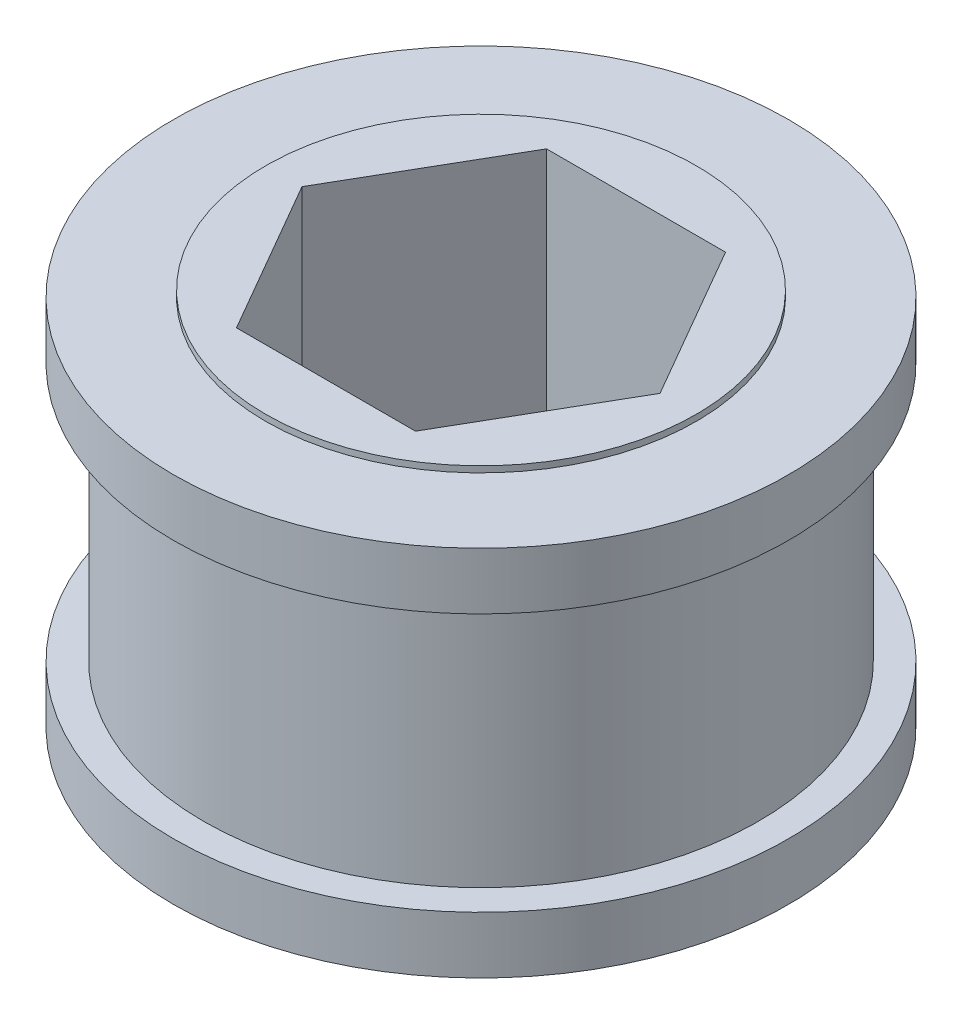
SolidWorks part; units mm, degrees
ref_plane "Front Plane" through (0, 0, 0) normal (0, 0, 1) x (1, 0, 0)
ref_plane "Top Plane" through (0, 0, 0) normal (0, 1, 0) x (1, 0, 0)
ref_plane "Right Plane" through (0, 0, 0) normal (1, 0, 0) x (0, 0, -1)
ref_axis "Axis1" through (0, 55, 0) along (0, -1, 0)
sketch "Sketch2" plane through (0, 0, 0) normal (1, 0, 0) x (0, 0, -1)
  line L0 (2.54, -3.2131) -> (8.89, -3.2131)
  line L1 (8.89, -3.2131) -> (8.89, -3.4671)
  line L2 (8.89, -3.4671) -> (12.7, -3.4671)
  line L3 (12.7, -3.4671) -> (12.7, -5.8166)
  line L5 (11.4554, -5.8166) -> (11.4554, -16.4846)
  line L7 (12.7, -16.4846) -> (12.7, -18.8341)
  line L8 (12.7, -18.8341) -> (8.89, -18.8341)
  line L9 (8.89, -18.8341) -> (8.89, -19.0881)
  line L10 (8.89, -19.0881) -> (2.54, -19.0881)
  line L11 (11.4554, -5.8166) -> (12.7, -5.8166)
  line L13 (2.54, -19.0881) -> (2.54, -3.2131)
  line L14 (0, 55) -> (0, -55) construction
  line L17 (11.4554, -16.4846) -> (12.7, -16.4846)
  dimension "D1" = 15.875
  dimension "D2" = 2.54
  dimension "D3" = 12.7
  dimension "D4" = 6.35
  dimension "D5" = 0.254
  dimension "D6" = 10.668
  dimension "D7" = 11.4554
revolve "Revolve1" add sketch "Sketch2" angle 360 about axis through (0, 55, 0) along (0, -1, 0)
sketch "Sketch3" plane through (0, -3.2131, 0) normal (0, 1, 0) x (1, 0, 0)
  line L1 (3.6955, 6.4008) -> (-3.6955, 6.4008)
  line L2 (-3.6955, 6.4008) -> (-7.391, 0)
  line L3 (-7.391, 0) -> (-3.6955, -6.4008)
  line L4 (-3.6955, -6.4008) -> (3.6955, -6.4008)
  line L5 (3.6955, -6.4008) -> (7.391, 0)
  line L6 (7.391, 0) -> (3.6955, 6.4008)
  circle A0 centre (0, 0) radius 6.4008 construction
  dimension "D1" = 12.8016
extrude "Cut-Extrude1" cut sketch "Sketch3" against normal through all both and the other way through all
